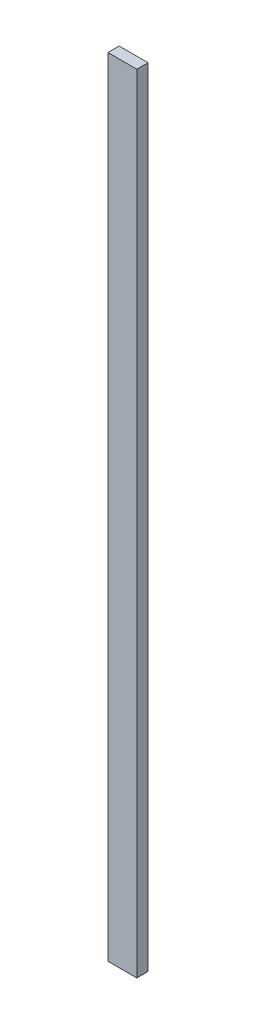
SolidWorks part; units mm, degrees
ref_plane "Front Plane" through (0, 0, 0) normal (0, 0, 1) x (1, 0, 0)
ref_plane "Top Plane" through (0, 0, 0) normal (0, 1, 0) x (1, 0, 0)
ref_plane "Right Plane" through (0, 0, 0) normal (1, 0, 0) x (0, 0, -1)
sketch "Sketch1" plane through (0, 0, 0) normal (0, 0, 1) x (1, 0, 0)
  line L1 (-69.5638, 644.9925) -> (-43.8222, 644.9925)
  line L2 (-69.5638, 644.9925) -> (-69.5638, -55.0075)
  line L3 (-69.5638, -55.0075) -> (-43.8222, -55.0075)
  line L4 (-43.8222, 644.9925) -> (-43.8222, -55.0075)
  point P4 (-43.8222, -55.0075)
  dimension "D1" = 700
extrude "Boss-Extrude1" add sketch "Sketch1" along normal blind 10
